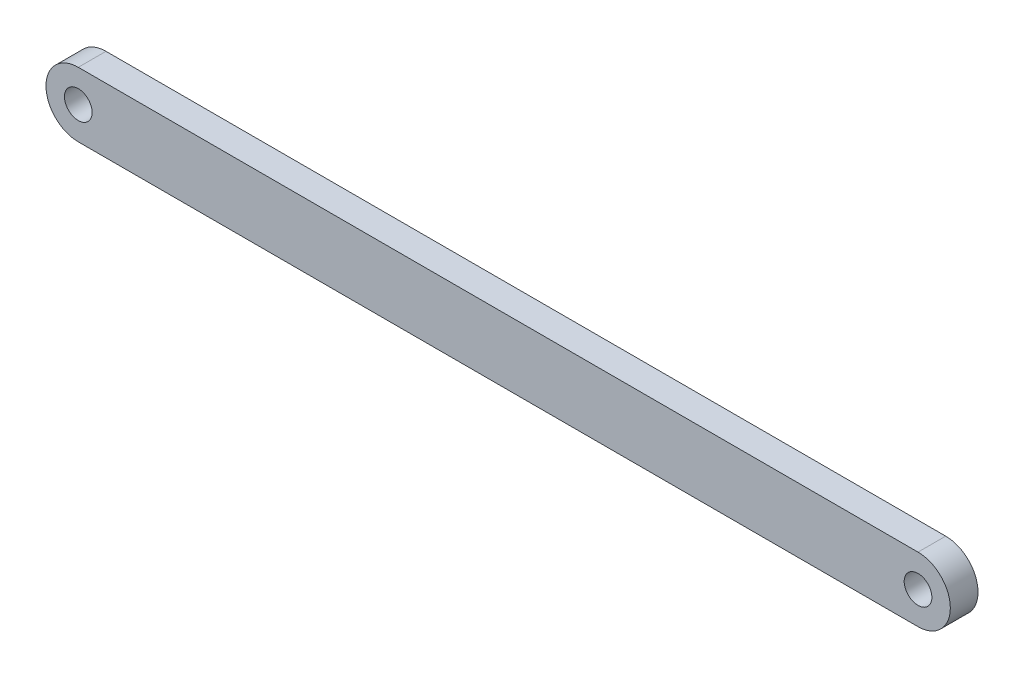
SolidWorks part; units mm, degrees
material "Thornel Mat VMA"
ref_plane "前视基准面" through (0, 0, 0) normal (0, 0, 1) x (1, 0, 0)
ref_plane "上视基准面" through (0, 0, 0) normal (0, 1, 0) x (1, 0, 0)
ref_plane "右视基准面" through (0, 0, 0) normal (1, 0, 0) x (0, 0, -1)
sketch "草图1" plane through (0, 0, 0) normal (0, 0, 1) x (1, 0, 0)
  line L0 (0, 0) -> (182, 0) construction
  line L1 (0, 7) -> (182, 7)
  line L2 (0, -7) -> (182, -7)
  line L3 (113.5, 0) -> (68.5, 0) construction
  line L4 (113.5, -3.5) -> (68.5, -3.5) construction
  line L5 (113.5, 3.5) -> (68.5, 3.5) construction
  line L6 (170.5, 3.5) -> (125.5, 3.5) construction
  line L7 (170.5, -3.5) -> (125.5, -3.5) construction
  line L8 (170.5, 0) -> (125.5, 0) construction
  line L9 (56.5, 3.5) -> (11.5, 3.5) construction
  line L10 (56.5, -3.5) -> (11.5, -3.5) construction
  line L11 (56.5, 0) -> (11.5, 0) construction
  arc A0 (0, 7) -> (0, -7) centre (0, 0) ccw
  arc A1 (182, -7) -> (182, 7) centre (182, 0) ccw
  circle A2 centre (0, 0) radius 3
  circle A3 centre (182, 0) radius 3
  arc A4 (113.5, -3.5) -> (113.5, 3.5) centre (113.5, 0) ccw construction
  arc A5 (68.5, 3.5) -> (68.5, -3.5) centre (68.5, 0) ccw construction
  arc A6 (170.5, -3.5) -> (170.5, 3.5) centre (170.5, 0) ccw construction
  arc A7 (125.5, 3.5) -> (125.5, -3.5) centre (125.5, 0) ccw construction
  arc A8 (56.5, -3.5) -> (56.5, 3.5) centre (56.5, 0) ccw construction
  arc A9 (11.5, 3.5) -> (11.5, -3.5) centre (11.5, 0) ccw construction
  point P3 (91, 0)
  point P14 (91, 0)
  point P23 (148, 0)
  point P29 (34, 0)
  dimension "D1" = 6
  dimension "D3" = 7
  dimension "D5" = 45
  dimension "D2" = 182
  dimension "D4" = 3.5
  dimension "D7" = 57
  dimension "D9" = 57
  dimension "D6" = 2
  dimension "D8" = 2
extrude "凸台-拉伸1" add sketch "草图1" along normal blind 6
